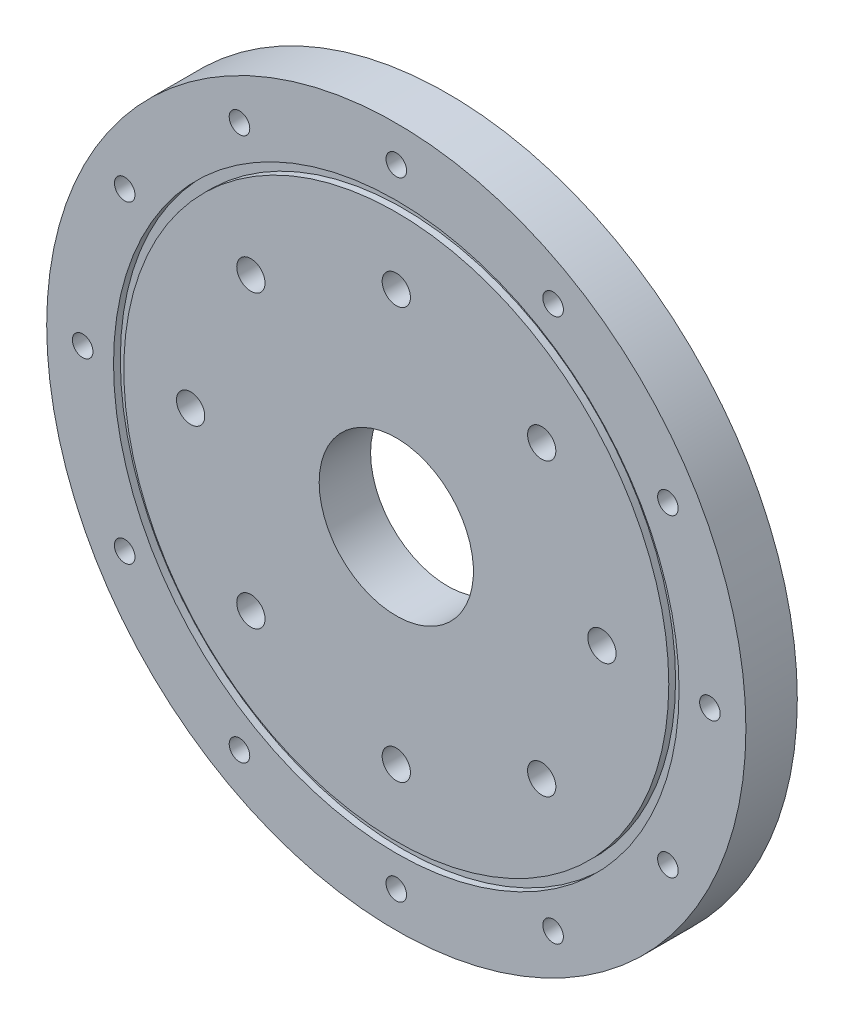
SolidWorks part; units mm, degrees
material "Malleable Cast Iron"
ref_plane "Front Plane" through (0, 0, 0) normal (0, 0, 1) x (1, 0, 0)
ref_plane "Top Plane" through (0, 0, 0) normal (0, 1, 0) x (1, 0, 0)
ref_plane "Right Plane" through (0, 0, 0) normal (1, 0, 0) x (0, 0, -1)
sketch "Sketch1" plane through (0, 0, 0) normal (0, 0, 1) x (1, 0, 0)
  circle A0 centre (0, 0) radius 75
  dimension "D1" = 150
extrude "Boss-Extrude1" add sketch "Sketch1" along normal blind 10
sketch "Sketch3" plane through (0, 0, 10) normal (0, 0, 1) x (1, 0, 0)
  circle A0 centre (0, 0) radius 4.5
  dimension "D1" = 9
extrude "Cut-Extrude2" cut sketch "Sketch3" against normal blind 10
sketch "Sketch5" plane through (0, 0, 0) normal (1, 0, 0) x (0, 0, -1)
  line L0 (0, -75) -> (0, 75) construction
  line L1 (0, 27.1526) -> (-2.667, 27.1526)
  line L2 (0, 27.1526) -> (0, 22.5806)
  line L3 (0, 22.5806) -> (-2.667, 22.5806)
  line L4 (-2.667, 27.1526) -> (-2.667, 22.5806)
  line L5 (0, 0) -> (16.8005, 0) construction
  dimension "D1" = 22.5806
  dimension "D2" = 4.572
  dimension "D3" = 2.667
revolve "Cut-Revolve1" cut sketch "Sketch5" angle 360 about L5
sketch "Sketch6" plane through (0, 0, 10) normal (0, 0, 1) x (1, 0, 0)
  circle A0 centre (0, 0) radius 53
  circle A1 centre (0, 0) radius 55
  dimension "D1" = 106
  dimension "D2" = 110
extrude "Cut-Extrude3" cut sketch "Sketch6" against normal blind 1.3208
sketch "Sketch10" plane through (0, 0, 0) normal (0, 0, -1) x (-1, 0, 0)
  circle A0 centre (0, 61) radius 2
  dimension "D1" = 4
  dimension "D2" = 61
extrude "Cut-Extrude6" cut sketch "Sketch10" against normal through all
hole_wizard "CBORE for M5 Hex Head Bolt1" positions "Sketch11" profile "Sketch13" counterbore size "M5" standard "ISO" end condition through all
sketch "Sketch11" plane through (0, 0, 0) normal (0, 0, -1) x (-1, 0, 0)
  line L0 (0, 0) -> (-28.2843, 28.2843) construction
  line L3 (0, 0) -> (-37.6217, 0) construction
  point P0 (-28.2843, 28.2843)
  dimension "D1" = 40
  dimension "D2" = 45
sketch "Sketch13" plane through (28.2843, 28.2843, 0) normal (1, 0, 0) x (0, 1, 0)
  line L0 (0, 0) -> (0, 10)
  line L1 (0, 10) -> (2.75, 10)
  line L3 (2.75, 10) -> (2.75, 3.5)
  line L4 (2.75, 3.5) -> (6.119, 3.5)
  line L5 (6.119, 3.5) -> (6.119, 0)
  line L7 (6.119, 0) -> (0, 0)
  line L11 (0, -6.35) -> (0, 107.95) construction
  dimension "Thru Hole Dia." = 5.5
  dimension "Thru Hole Depth" = 10
  dimension "C'Bore Dia." = 12.238
  dimension "C'Bore Depth" = 3.5
sketch "Sketch16" plane through (0, 0, 0) normal (0, 0, -1) x (-1, 0, 0)
  circle A0 centre (0, 0) radius 68
  circle A1 centre (0, 0) radius 75
  dimension "D1" = 136
extrude "Cut-Extrude10" cut sketch "Sketch16" against normal blind 10
pattern_circular "CirPattern1" count 12 over 360 about axis through (0, 0, 0) along (0, 0, 1) of "Cut-Extrude6"
pattern_circular "CirPattern2" count 8 over 360 about axis through (0, 0, 0) along (0, 0, 1) of "CBORE for M5 Hex Head Bolt1"
sketch "Sketch17" plane through (0, 0, 0) normal (0, 0, -1) x (-1, 0, 0)
  circle A0 centre (-28.2843, 28.2843) radius 6.119
extrude "Cut-Extrude11" cut sketch "Sketch17" against normal blind 5 contours A0
pattern_circular "CirPattern3" count 8 over 360 about axis through (0, 0, 0) along (0, 0, -1) of "Cut-Extrude11"
sketch "Sketch18" plane through (0, 0, 0) normal (0, 0, -1) x (-1, 0, 0)
  circle A0 centre (0, 0) radius 15
  dimension "D1" = 30
extrude "Cut-Extrude12" cut sketch "Sketch18" against normal blind 10
